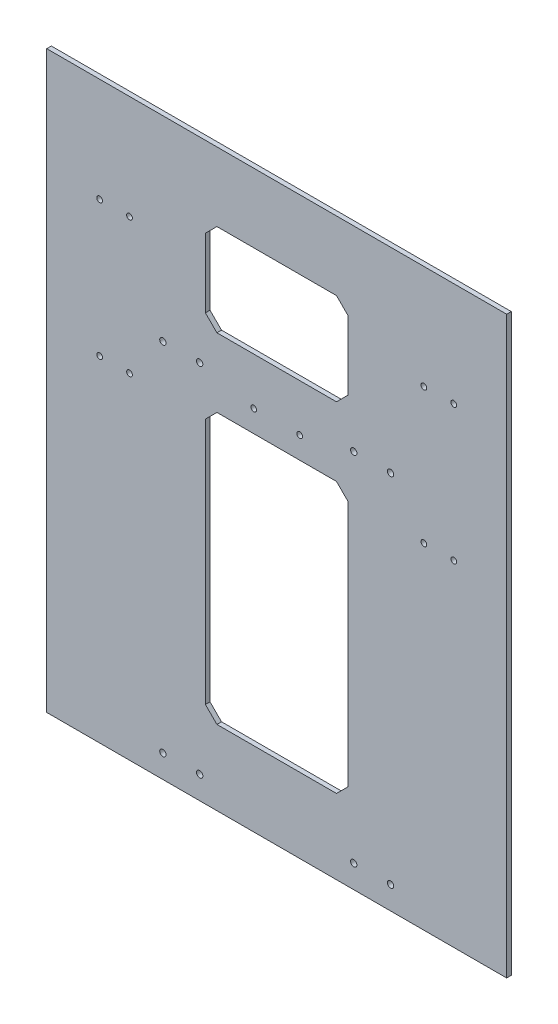
SolidWorks part; units mm, degrees
material "1023 Carbon Steel Sheet (SS)"
ref_plane "Plan de face" through (0, 0, 0) normal (0, 0, 1) x (1, 0, 0)
ref_plane "Plan de dessus" through (0, 0, 0) normal (0, 1, 0) x (1, 0, 0)
ref_plane "Plan de droite" through (0, 0, 0) normal (1, 0, 0) x (0, 0, -1)
sketch "Sketch1" plane through (0, 0, 0) normal (0, 0, 1) x (1, 0, 0)
  line L1 (0, 0) -> (400, 0)
  line L2 (0, 0) -> (0, 500)
  line L3 (0, 500) -> (400, 500)
  line L4 (400, 0) -> (400, 500)
  dimension "D1" = 400
  dimension "D2" = 500
extrude "Boss-Extrude1" add sketch "Sketch1" along normal blind 4
sketch "Sketch2" plane through (0, 0, 4) normal (0, 0, 1) x (1, 0, 0)
  line L1 (138, 300) -> (262, 300)
  line L2 (138, 300) -> (138, 65)
  line L3 (138, 65) -> (262, 65)
  line L4 (262, 300) -> (262, 65)
  line L5 (200, 65) -> (200, 0) construction
  line L6 (0, 0) -> (400, 0) construction
  line L7 (400, 500) -> (0, 500) construction
  line L8 (0, 0) -> (400, 0) construction
  dimension "D1" = 124
  dimension "D3" = 65
  dimension "D4" = 200
extrude "Cut-Extrude1" cut sketch "Sketch2" against normal through all contours L4 L3 L2 L1
sketch "Sketch4" plane through (0, 0, 4) normal (0, 0, 1) x (1, 0, 0)
  line L0 (283, 227.677) -> (283, 330) construction
  line L1 (200, 500) -> (200, 363.1163) construction
  line L2 (400, 0) -> (400, 500) construction
  line L3 (400, 500) -> (0, 500) construction
  circle A0 centre (299, 330) radius 2.75
  circle A1 centre (267, 330) radius 2.75
  circle A2 centre (133, 330) radius 2.75
  circle A3 centre (101, 330) radius 2.75
  dimension "D1" = 5.5
  dimension "D2" = 170
  dimension "D3" = 101
extrude "Cut-Extrude3" cut sketch "Sketch4" against normal blind 10 contours A2
sketch "Sketch5" plane through (0, 0, 4) normal (0, 0, 1) x (1, 0, 0)
  line L0 (200, 500) -> (200, 346.7251) construction
  line L1 (400, 500) -> (0, 500) construction
  line L2 (400, 500) -> (0, 500) construction
  line L3 (0, 500) -> (0, 0) construction
  circle A0 centre (180, 319) radius 2.5
  circle A1 centre (220, 319) radius 2.5
  dimension "D1" = 5
  dimension "D2" = 181
  dimension "D3" = 180
extrude "Cut-Extrude4" cut sketch "Sketch5" against normal through all
sketch "Sketch6" plane through (0, 0, 4) normal (0, 0, 1) x (1, 0, 0)
  line L0 (200, 500) -> (200, 366.1728) construction
  line L2 (400, 500) -> (0, 500) construction
  line L3 (0, 500) -> (0, 0) construction
  circle A0 centre (72, 409.5) radius 2.5
  circle A1 centre (46, 409.5) radius 2.5
  circle A2 centre (72, 291.5) radius 2.5
  circle A3 centre (46, 291.5) radius 2.5
  circle A4 centre (328, 291.5) radius 2.5
  circle A5 centre (354, 291.5) radius 2.5
  circle A6 centre (328, 409.5) radius 2.5
  circle A7 centre (354, 409.5) radius 2.5
  dimension "D1" = 5
  dimension "D2" = 5
  dimension "D3" = 5
  dimension "D4" = 5
  dimension "D5" = 90.5
  dimension "D6" = 118
  dimension "D7" = 46
  dimension "D8" = 26
extrude "Cut-Extrude5" cut sketch "Sketch6" against normal up to surface (4 mm away) up to face at (217.5, 319, 0)
sketch "Sketch7" plane through (0, 0, 0) normal (0, 0, -1) x (-1, 0, 0)
  line L0 (-400, 0) -> (-400, 500) construction
  line L1 (0, 0) -> (-400, 0) construction
  line L2 (-283, 20) -> (-283, 26.6916) construction
  line L3 (-200, 50) -> (-200, 0) construction
  circle A0 centre (-299, 20) radius 2.75
  circle A1 centre (-267, 20) radius 2.75
  circle A2 centre (-299, 20) radius 2.75
  circle A3 centre (-267, 20) radius 2.75
  circle A4 centre (-299, 20) radius 2.75
  circle A5 centre (-267, 20) radius 2.75
  circle A6 centre (-299, 20) radius 2.75
  circle A7 centre (-267, 20) radius 2.75
  circle A8 centre (-133, 20) radius 2.75
  circle A9 centre (-101, 20) radius 2.75
  circle A10 centre (-133, 20) radius 2.75
  circle A11 centre (-101, 20) radius 2.75
  circle A12 centre (-133, 20) radius 2.75
  circle A13 centre (-101, 20) radius 2.75
  circle A14 centre (-133, 20) radius 2.75
  circle A15 centre (-101, 20) radius 2.75
  dimension "D2" = 5.5
  dimension "D1" = 101
  dimension "D3" = 20
  dimension "D4" = 16
extrude "Cut-Extrude6" cut sketch "Sketch7" against normal blind 4 contours A1 | A0 | A8 | A9
sketch "Sketch8" plane through (0, 0, 0) normal (0, 0, -1) x (-1, 0, 0)
  line L0 (-138, 300) -> (-43.5209, 182.5)
  line L1 (-43.5209, 182.5) -> (-138, 65)
  line L2 (-138, 65) -> (-262, 65)
  line L3 (-262, 65) -> (-348.7947, 182.5)
  line L4 (-348.7947, 182.5) -> (-262, 300)
  line L5 (-262, 300) -> (-138, 300)
  dimension "D1" = 117.5
extrude "Cut-Extrude8" [suppressed] cut sketch "Sketch8" against normal blind 4
sketch "Sketch9" plane through (0, 0, 0) normal (0, 0, -1) x (-1, 0, 0)
  line L0 (-400, 500) -> (0, 500) construction
  line L1 (-262, 360) -> (-138, 360)
  line L2 (-262, 360) -> (-262, 440)
  line L3 (-262, 440) -> (-138, 440)
  line L4 (-138, 360) -> (-138, 440)
  line L5 (-262, 360) -> (-138, 440) construction
  line L6 (-262, 440) -> (-138, 360) construction
  line L8 (-400, 0) -> (-400, 500) construction
  point P0 (-200, 400)
  dimension "D1" = 100
  dimension "D2" = 124
  dimension "D3" = 80
  dimension "D4" = 200
extrude "Cut-Extrude9" cut sketch "Sketch9" against normal blind 4
chamfer "Chamfer1" distance 10 angle 45 8 edges at (138, 360, 2) (138, 440, 2) (262, 440, 2) (262, 360, 2) (138, 65, 2) (262, 300, 2) (138, 300, 2) (262, 65, 2)
